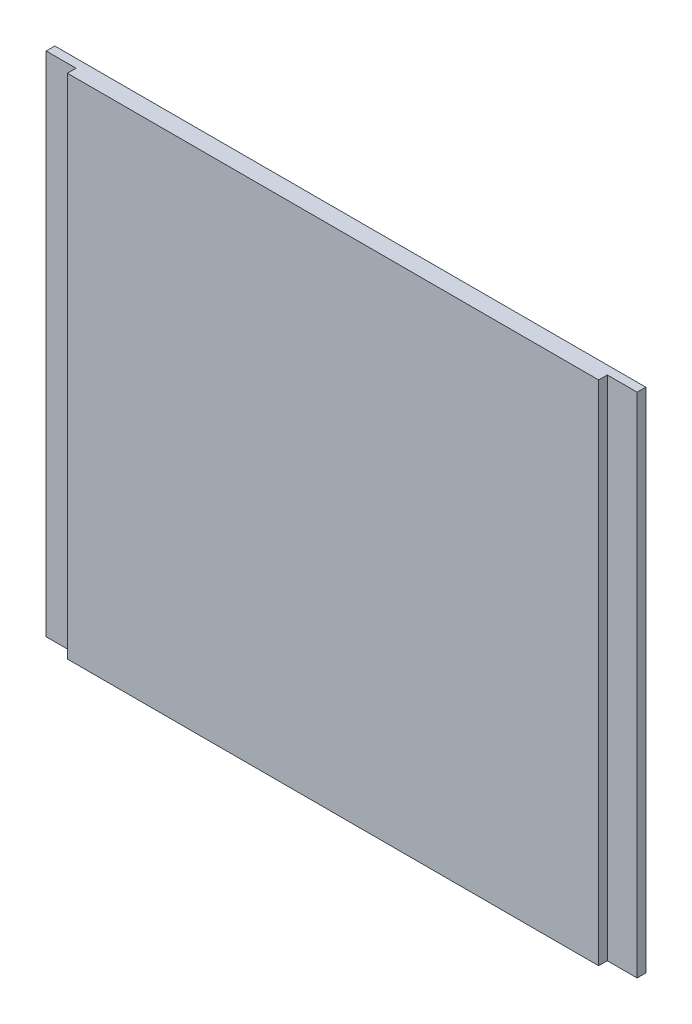
SolidWorks part; units mm, degrees
ref_plane "Front Plane" through (0, 0, 0) normal (0, 0, 1) x (1, 0, 0)
ref_plane "Top Plane" through (0, 0, 0) normal (0, 1, 0) x (1, 0, 0)
ref_plane "Right Plane" through (0, 0, 0) normal (1, 0, 0) x (0, 0, -1)
sketch "Sketch2" plane through (0, 0, 0) normal (0, 1, 0) x (1, 0, 0)
  line L0 (-54.3137, 1.45) -> (44.6863, 1.45)
  line L1 (44.6863, 1.45) -> (44.6863, 0)
  line L2 (44.6863, 0) -> (39.6863, 0)
  line L3 (39.6863, 0) -> (39.6863, -1.45)
  line L4 (39.6863, -1.45) -> (-49.3137, -1.45)
  line L5 (-49.3137, -1.45) -> (-49.3137, 0)
  line L6 (-49.3137, 0) -> (-54.3137, 0)
  line L7 (-54.3137, 0) -> (-54.3137, 1.45)
  dimension "D1" = 99
  dimension "D2" = 89
  dimension "D3" = 5
  dimension "D4" = 1.45
  dimension "D5" = 1.45
  dimension "D6" = 1.45
extrude "Boss-Extrude1" add sketch "Sketch2" along normal blind 85
